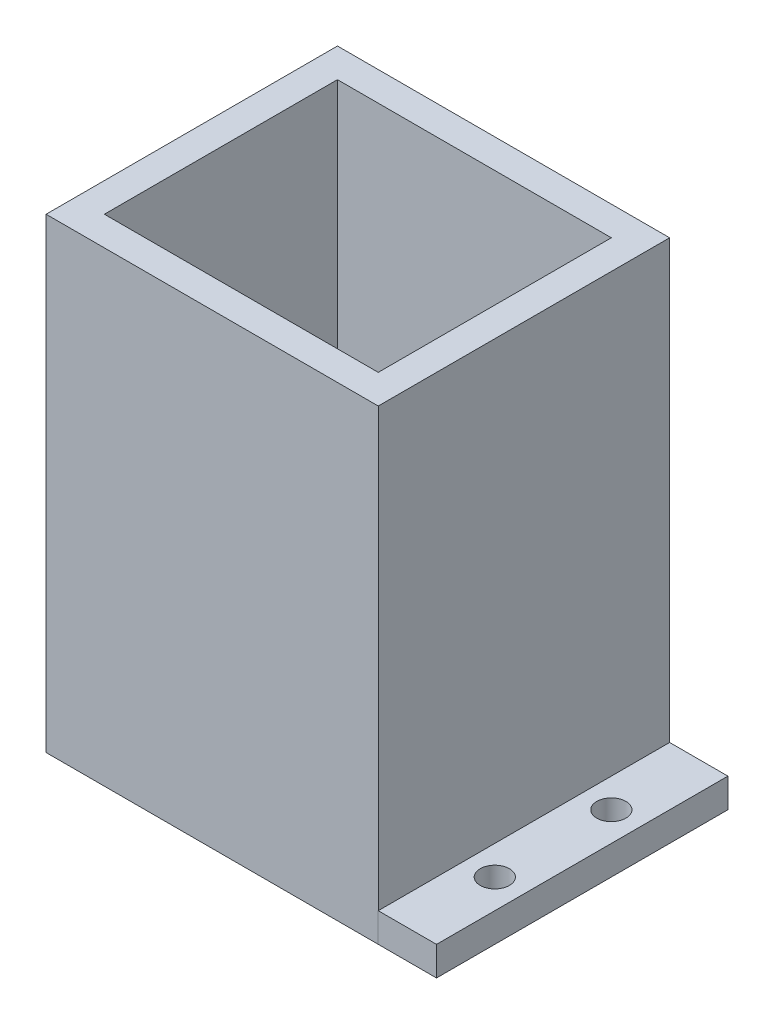
SolidWorks part; units mm, degrees
ref_plane "Front Plane" through (0, 0, 0) normal (0, 0, 1) x (1, 0, 0)
ref_plane "Top Plane" through (0, 0, 0) normal (0, 1, 0) x (1, 0, 0)
ref_plane "Right Plane" through (0, 0, 0) normal (1, 0, 0) x (0, 0, -1)
sketch "Sketch1" plane through (0, 0, 0) normal (0, 1, 0) x (1, 0, 0)
  line L1 (-3.2818, 2.453) -> (53.7182, 2.453)
  line L2 (-3.2818, 2.453) -> (-3.2818, -47.547)
  line L3 (-3.2818, -47.547) -> (53.7182, -47.547)
  line L4 (53.7182, 2.453) -> (53.7182, -47.547)
  dimension "D1" = 50
  dimension "D2" = 57
extrude "Boss-Extrude1" add sketch "Sketch1" along normal blind 80
sketch "Sketch2" plane through (0, 80, 0) normal (0, 1, 0) x (1, 0, 0)
  line L0 (53.7182, 2.453) -> (-3.2818, 2.453) construction
  line L1 (1.7182, -2.547) -> (48.7182, -2.547)
  line L2 (1.7182, -2.547) -> (1.7182, -42.547)
  line L3 (1.7182, -42.547) -> (48.7182, -42.547)
  line L4 (48.7182, -2.547) -> (48.7182, -42.547)
  line L5 (53.7182, -47.547) -> (53.7182, 2.453) construction
  dimension "D1" = 47
  dimension "D2" = 40
  dimension "D3" = 5
  dimension "D4" = 5
extrude "Cut-Extrude1" cut sketch "Sketch2" against normal blind 75
sketch "Sketch3" plane through (0, 0, 0) normal (0, 1, 0) x (1, 0, 0)
  line L1 (53.7182, 2.453) -> (63.7182, 2.453)
  line L2 (53.7182, 2.453) -> (53.7182, -47.5511)
  line L3 (53.7182, -47.5511) -> (63.7182, -47.5511)
  line L4 (63.7182, 2.453) -> (63.7182, -47.5511)
  circle A0 centre (58.7182, -12.5511) radius 2.5
  circle A1 centre (58.7182, -32.5511) radius 2.5
  dimension "D3" = 5
  dimension "D4" = 5
  dimension "D1" = 20
  dimension "D2" = 15
  dimension "D5" = 10
  dimension "D6" = 5
extrude "Boss-Extrude2" add sketch "Sketch3" along normal blind 5
